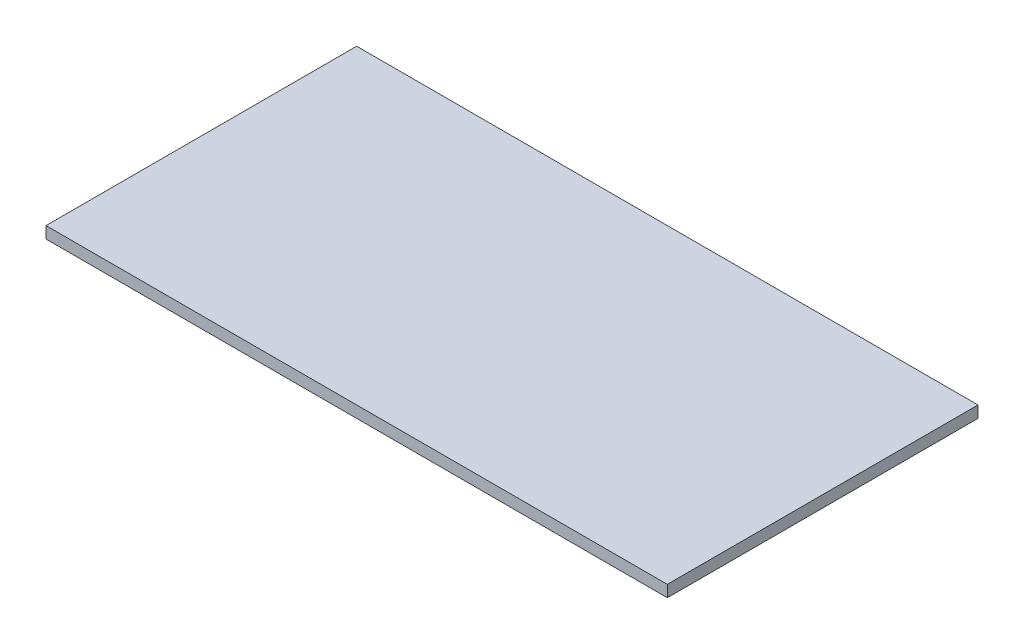
SolidWorks part; units mm, degrees
ref_plane "Front Plane" through (0, 0, 0) normal (0, 0, 1) x (1, 0, 0)
ref_plane "Top Plane" through (0, 0, 0) normal (0, 1, 0) x (1, 0, 0)
ref_plane "Right Plane" through (0, 0, 0) normal (1, 0, 0) x (0, 0, -1)
sketch "Sketch1" plane through (0, 0, 0) normal (0, 1, 0) x (1, 0, 0)
  line L1 (0, 0) -> (800, 0)
  line L2 (0, 0) -> (0, 400)
  line L3 (0, 400) -> (800, 400)
  line L4 (800, 0) -> (800, 400)
  dimension "D1" = 400
  dimension "D2" = 800
extrude "Boss-Extrude1" add sketch "Sketch1" along normal blind 15
